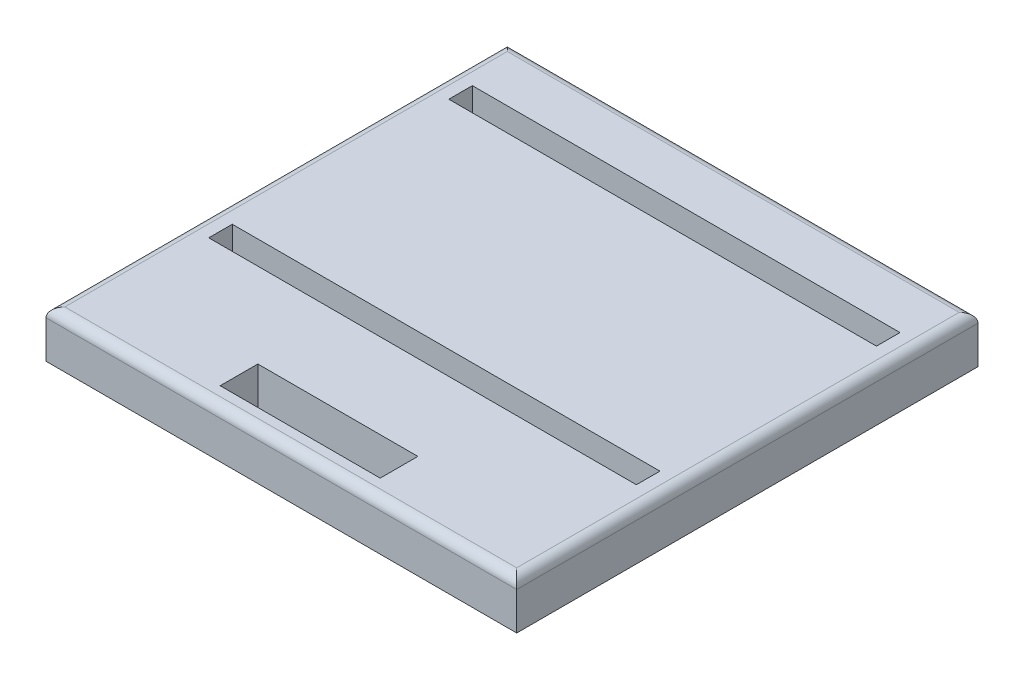
SolidWorks part; units mm, degrees
ref_plane "Front Plane" through (0, 0, 0) normal (0, 0, 1) x (1, 0, 0)
ref_plane "Top Plane" through (0, 0, 0) normal (0, 1, 0) x (1, 0, 0)
ref_plane "Right Plane" through (0, 0, 0) normal (1, 0, 0) x (0, 0, -1)
sketch "Sketch2" plane through (0, 0, 0) normal (0, 1, 0) x (1, 0, 0)
  line L0 (0, 242.4303) -> (0, -237.7501) construction
  line L1 (-63.5, 81.28) -> (-63.5, -43.18)
  line L2 (-63.5, 81.28) -> (63.5, 81.28)
  line L3 (-63.5, -43.18) -> (63.5, -43.18)
  line L4 (63.5, 81.28) -> (63.5, -43.18)
  dimension "D1" = 127
  dimension "D2" = 63.5
  dimension "D3" = 124.46
  dimension "D4" = 43.18
extrude "Boss-Extrude1" add sketch "Sketch2" along normal blind 12.7
fillet "Fillet1" radius 2.54 4 edges at (63.5, 12.7, -19.05) (-63.5, 12.7, -19.05) (0, 12.7, 43.18) (0, 12.7, -81.28)
sketch "Sketch3" plane through (0, 12.7, 0) normal (0, 1, 0) x (1, 0, 0)
  line L0 (57.6928, 59.69) -> (57.6928, 66.04)
  line L1 (57.6928, 59.69) -> (-57.6928, 59.69)
  line L2 (57.6928, 66.04) -> (-57.6928, 66.04)
  line L3 (-57.6928, 59.69) -> (-57.6928, 66.04)
  line L4 (-21.59, -38.1) -> (-21.59, -27.94)
  line L5 (63.5, 81.28) -> (63.5, -43.18) construction
  line L6 (-63.5, 81.28) -> (63.5, 81.28) construction
  line L7 (-60.96, -40.64) -> (60.96, -40.64) construction
  line L8 (-21.59, -27.94) -> (21.59, -27.94)
  line L9 (21.59, -27.94) -> (21.59, -38.1)
  line L10 (57.6928, 1.27) -> (57.6928, -5.08)
  line L11 (57.6928, -5.08) -> (-57.6928, -5.08)
  line L12 (-57.6928, 1.27) -> (-57.6928, -5.08)
  line L13 (57.6928, 1.27) -> (-57.6928, 1.27)
  line L14 (21.59, -38.1) -> (-21.59, -38.1)
  line L17 (60.96, -40.64) -> (60.96, 78.74) construction
  dimension "D1" = 115.3856
  dimension "D2" = 5.8072
  dimension "D3" = 15.24
  dimension "D4" = 6.35
  dimension "D5" = 35.56
  dimension "D6" = 39.37
  dimension "D7" = 43.18
  dimension "D8" = 2.54
  dimension "D9" = 10.16
extrude "Cut-Extrude1" cut sketch "Sketch3" against normal blind 12.7
